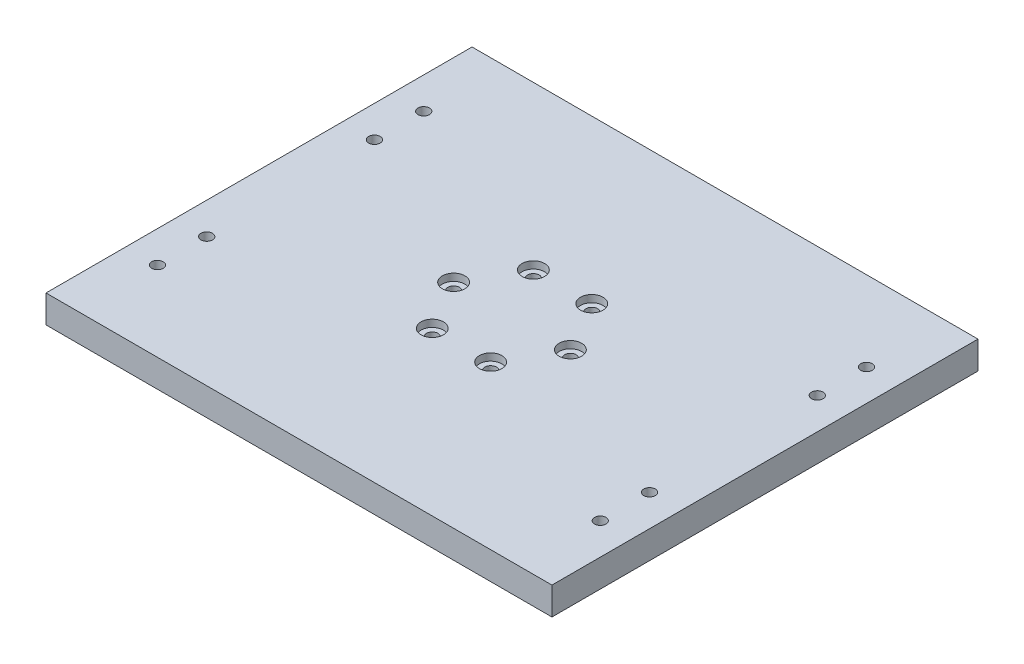
SolidWorks part; units mm, degrees
ref_plane "Front Plane" through (0, 0, 0) normal (0, 0, 1) x (1, 0, 0)
ref_plane "Top Plane" through (0, 0, 0) normal (0, 1, 0) x (1, 0, 0)
ref_plane "Right Plane" through (0, 0, 0) normal (1, 0, 0) x (0, 0, -1)
sketch "Sketch1" plane through (0, 0, 0) normal (0, 1, 0) x (1, 0, 0)
  line L1 (-241.3, -203.2) -> (241.3, -203.2)
  line L2 (-241.3, -203.2) -> (-241.3, 203.2)
  line L3 (-241.3, 203.2) -> (241.3, 203.2)
  line L4 (241.3, -203.2) -> (241.3, 203.2)
  line L5 (-241.3, -203.2) -> (241.3, 203.2) construction
  line L6 (-241.3, 203.2) -> (241.3, -203.2) construction
  point P0 (0, 0)
  dimension "D1" = 406.4
  dimension "D2" = 482.6
extrude "Boss-Extrude1" add sketch "Sketch1" along normal blind 26.416
sketch "Sketch3" plane through (0, 26.416, 0) normal (0, 1, 0) x (1, 0, 0)
  line L1 (-236.601, -67.31) -> (-160.401, -67.31) construction
  line L2 (-236.601, -67.31) -> (-236.601, -92.71) construction
  line L3 (-236.601, -92.71) -> (-160.401, -92.71) construction
  line L4 (-160.401, -67.31) -> (-160.401, -92.71) construction
  line L5 (-236.601, -67.31) -> (-160.401, -92.71) construction
  line L6 (-236.601, -92.71) -> (-160.401, -67.31) construction
  line L7 (-241.3, 203.2) -> (-241.3, -203.2) construction
  line L8 (0, 203.2) -> (0, -188.1619) construction
  line L9 (241.3, 203.2) -> (-241.3, 203.2) construction
  line L10 (-241.3, 0) -> (265.7597, 0) construction
  line L11 (-236.601, 92.71) -> (-160.401, 92.71) construction
  line L12 (-160.401, 67.31) -> (-160.401, 92.71) construction
  line L13 (-236.601, 67.31) -> (-160.401, 67.31) construction
  line L14 (-236.601, 67.31) -> (-236.601, 92.71) construction
  line L15 (236.601, -92.71) -> (160.401, -92.71) construction
  line L16 (160.401, -67.31) -> (160.401, -92.71) construction
  line L17 (236.601, -67.31) -> (160.401, -67.31) construction
  line L18 (236.601, -67.31) -> (236.601, -92.71) construction
  line L19 (236.601, 67.31) -> (236.601, 92.71) construction
  line L20 (236.601, 67.31) -> (160.401, 67.31) construction
  line L21 (160.401, 67.31) -> (160.401, 92.71) construction
  line L22 (236.601, 92.71) -> (160.401, 92.71) construction
  circle A0 centre (-211.201, -80.01) radius 1.27
  circle A2 centre (-211.201, 80.01) radius 1.27
  circle A5 centre (211.201, -80.01) radius 1.27
  circle A6 centre (211.201, 80.01) radius 1.27
  circle A15 centre (55.7, 0) radius 5.25
  circle A16 centre (27.85, -48.2376) radius 5.25
  circle A17 centre (-27.85, -48.2376) radius 5.25
  circle A18 centre (-55.7, 0) radius 5.25
  circle A19 centre (-27.85, 48.2376) radius 5.25
  circle A20 centre (27.85, 48.2376) radius 5.25
  circle A21 centre (-211.201, -127) radius 1.27
  circle A22 centre (211.201, -127) radius 1.27
  circle A23 centre (211.201, 127) radius 1.27
  circle A24 centre (-211.201, 127) radius 1.27
  point P0 (-198.501, -80.01)
  point P59 (0, 0)
  dimension "D5" = 25.4
  dimension "D6" = 46.99
  dimension "D7" = 2.54
  dimension "D8" = 55.7
  dimension "D9" = 10.5
  dimension "D1" = 76.2
  dimension "D2" = 25.4
  dimension "D3" = 80.01
  dimension "D4" = 236.601
extrude "Cut-Extrude2" cut sketch "Sketch3" against normal through all
hole_wizard "CBORE for M10 Hex Head Bolt1" positions "Sketch10" profile "Sketch11" counterbore size "M10" standard "ANSI Metric" end condition through all
sketch "Sketch10" plane through (0, 26.416, 0) normal (0, 1, 0) x (1, 0, 0)
  point P0 (27.85, 48.2376)
  point P3 (55.7, 0)
  point P6 (27.85, -48.2376)
  point P9 (-27.85, -48.2376)
  point P12 (-55.7, 0)
  point P15 (-27.85, 48.2376)
sketch "Sketch11" plane through (27.85, 26.416, -48.2376) normal (1, 0, 0) x (0, 0, 1)
  line L0 (0, 0) -> (0, 26.416)
  line L1 (0, 26.416) -> (5.5, 26.416)
  line L3 (5.5, 26.416) -> (5.5, 6.85)
  line L4 (5.5, 6.85) -> (10.74, 6.85)
  line L5 (10.74, 6.85) -> (10.74, 0)
  line L7 (10.74, 0) -> (0, 0)
  line L11 (0, -6.35) -> (0, 107.95) construction
  dimension "Thru Hole Dia." = 11
  dimension "Thru Hole Depth" = 26.416
  dimension "C'Bore Dia." = 21.48
  dimension "C'Bore Depth" = 6.85
hole_wizard "M10 Clearance Hole1" positions "Sketch14" profile "Sketch15" hole size "M10" standard "ANSI Metric" end condition through all
sketch "Sketch14" plane through (0, 26.416, 0) normal (0, 1, 0) x (1, 0, 0)
  point P0 (-211.201, 127)
  point P3 (-211.201, 80.01)
  point P6 (-211.201, -80.01)
  point P9 (-211.201, -127)
  point P12 (211.201, -127)
  point P15 (211.201, -80.01)
  point P18 (211.201, 80.01)
  point P21 (211.201, 127)
sketch "Sketch15" plane through (-211.201, 26.416, -127) normal (1, 0, 0) x (0, 0, 1)
  line L0 (0, 0) -> (0, 26.416)
  line L1 (0, 26.416) -> (5.5, 26.416)
  line L2 (5.5, 26.416) -> (5.5, 0)
  line L5 (5.5, 0) -> (0, 0)
  line L11 (0, -6.35) -> (0, 107.95) construction
  dimension "Thru Hole Dia." = 11
  dimension "Thru Hole Depth" = 26.416
